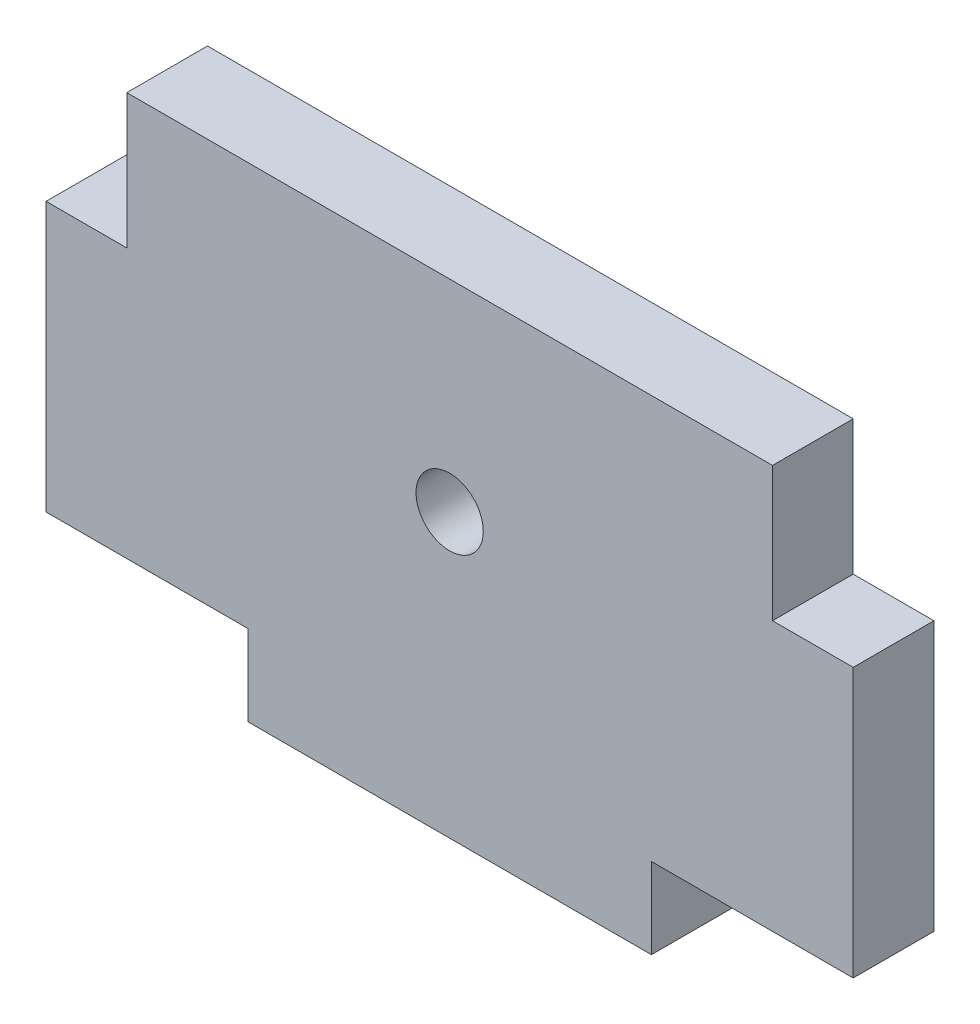
SolidWorks part; units mm, degrees
ref_plane "Front Plane" through (0, 0, 0) normal (0, 0, 1) x (1, 0, 0)
ref_plane "Top Plane" through (0, 0, 0) normal (0, 1, 0) x (1, 0, 0)
ref_plane "Right Plane" through (0, 0, 0) normal (1, 0, 0) x (0, 0, -1)
sketch "Sketch1" plane through (0, 0, 0) normal (0, 0, 1) x (1, 0, 0)
  line L1 (0, 0) -> (60, 0)
  line L2 (0, 0) -> (0, 36)
  line L3 (0, 36) -> (60, 36)
  line L4 (60, 0) -> (60, 36)
  dimension "D1" = 60
  dimension "D2" = 36
extrude "Boss-Extrude1" add sketch "Sketch1" along normal blind 6
sketch "Sketch2" plane through (0, 0, 6) normal (0, 0, 1) x (1, 0, 0)
  line L1 (0, 0) -> (15, 0)
  line L2 (0, 0) -> (0, 6)
  line L3 (0, 6) -> (15, 6)
  line L4 (15, 0) -> (15, 6)
  line L5 (60, 0) -> (45, 0)
  line L6 (60, 0) -> (60, 6)
  line L7 (60, 6) -> (45, 6)
  line L8 (45, 0) -> (45, 6)
  dimension "D1" = 15
  dimension "D2" = 6
extrude "Cut-Extrude1" cut sketch "Sketch2" against normal blind 6
sketch "Sketch3" plane through (0, 0, 6) normal (0, 0, 1) x (1, 0, 0)
  line L1 (0, 36) -> (6, 36)
  line L2 (0, 36) -> (0, 26)
  line L3 (0, 26) -> (6, 26)
  line L4 (6, 36) -> (6, 26)
  line L5 (60, 36) -> (54, 36)
  line L6 (60, 36) -> (60, 26)
  line L7 (60, 26) -> (54, 26)
  line L8 (54, 36) -> (54, 26)
  dimension "D1" = 6
  dimension "D2" = 10
extrude "Cut-Extrude2" cut sketch "Sketch3" against normal blind 6
sketch "Sketch4" plane through (0, 0, 6) normal (0, 0, 1) x (1, 0, 0)
  line L0 (54, 36) -> (6, 36) construction
  circle A0 centre (30, 21) radius 2.5
  point P4 (30, 36)
  dimension "D1" = 5
  dimension "D2" = 15
extrude "Cut-Extrude3" cut sketch "Sketch4" against normal blind 6
